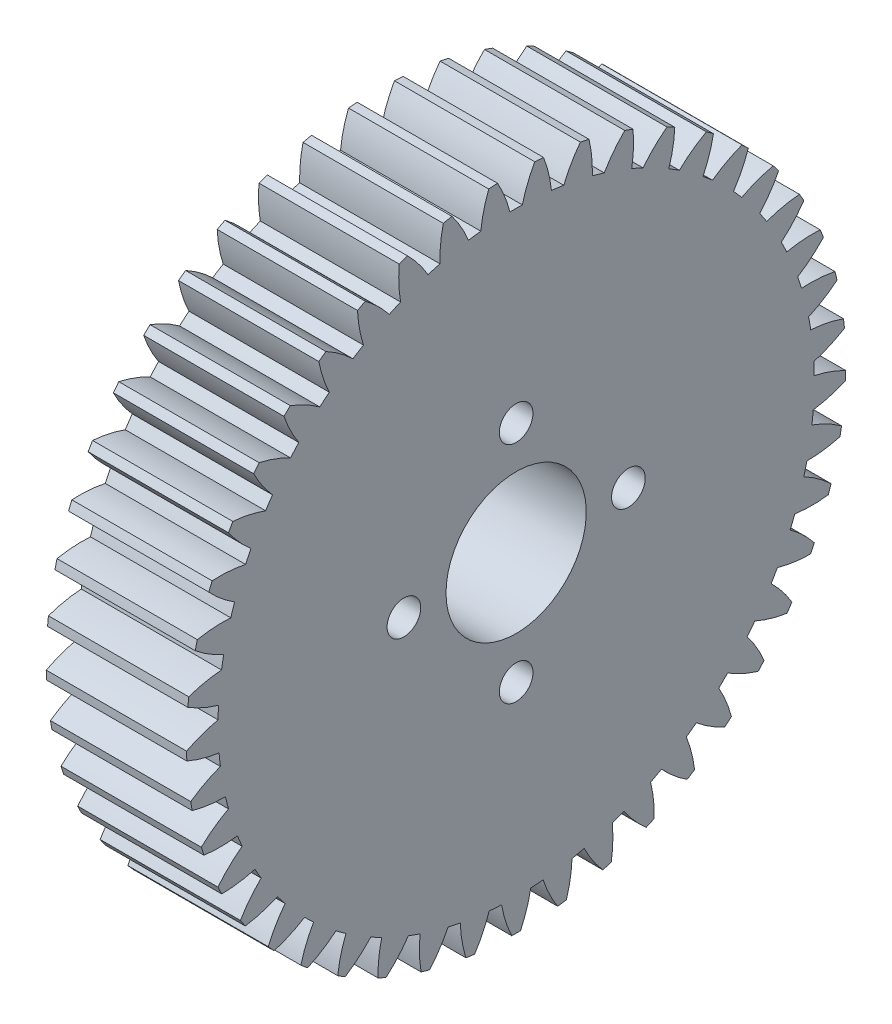
SolidWorks part; units mm, degrees
ref_plane "Plane1" through (0, 0, 0) normal (0, 0, 1) x (1, 0, 0)
ref_plane "Plane2" through (0, 0, 0) normal (0, 1, 0) x (1, 0, 0)
ref_plane "Plane3" through (0, 0, 0) normal (1, 0, 0) x (0, 0, -1)
sketch "HoldingSke" plane through (0, 0, 0) normal (0, 1, 0) x (1, 0, 0)
  line L0 (0, 0) -> (0.7071, -0.7071)
  line L1 (-15, 0) -> (100, 0) construction
  line L2 (0, 0) -> (-2.1039, 2.3779)
  line L3 (0, 0) -> (-11.863, 4.5341)
  line L4 (0, 0) -> (6.1066, 6.1066)
  line L5 (0, 0) -> (-46.8476, -17.4728)
  line L6 (0, 0) -> (-8.2896, -5.593)
  line L7 (-2.1039, 2.3779) -> (8.6586, 51.2059)
  line L8 (-76.2, 54.61) -> (-74.4, 54.61)
  line L9 (-71.009, 38.7566) -> (-53.1078, 45.2721)
  line L10 (-76.2, 71.12) -> (104.1128, 71.12)
  line L11 (0, 0) -> (-10, 0)
  line L12 (-76.2, 101.6) -> (-76.162, 101.6)
  line L13 (24.9733, 27.94) -> (52.9518, 28.4284)
  line L14 (24.9733, 27.94) -> (24.9743, 27.94)
  line L15 (24.9733, 27.94) -> (100.4006, 29.5858)
  line L16 (-63.627, -1) -> (-12.827, -1)
  circle A0 centre (0, 0) radius 5
  circle A1 centre (0, 0) radius 21.249
  circle A2 centre (0, 0) radius 37.5
  circle A3 centre (0, 0) radius 5
  dimension "MHD" = 42.498
  dimension "Hub_dia" = 75
  dimension "Bore" = 10
  dimension "MBD" = 10
  dimension "Num_teeth" = 45
  dimension "Pitch" = 1
  dimension "Overall_len" = 50
  dimension "Show_teeth" = 45
  dimension "Thickness" = 10
  dimension "OAL" = 50.0001
  dimension "T_dim" = 1.8
  dimension "Ap" = 20
  dimension "H" = 19.05
  dimension "Pitch_radius" = 180.3128
  dimension "Width" = 10
  dimension "Backlash" = 0.038
  dimension "Addendum_fac" = 1
  dimension "Dedendum_fac" = 1.25
  dimension "Clearance_fac" = 0.25
  dimension "Dedendum_add" = 0.001
  dimension "Module" = 1
sketch "BasProSke" plane through (0, 0, 0) normal (0, 1, 0) x (1, 0, 0)
  line L0 (-10, 0) -> (60, 0) construction
  line L1 (0, 0) -> (0, 23.5)
  line L2 (0, 0) -> (10, 0)
  line L3 (10, 0) -> (10, 23.5)
  line L4 (10, 23.5) -> (0, 23.5)
  dimension "Thickness" = 10
  dimension "Diameter" = 47
revolve "Base-Revolve" add sketch "BasProSke" angle 360 about L0
sketch "TooCutSke" plane through (0, 0, 0) normal (1, 0, 0) x (0, 0, -1)
  line L1 (0, 0) -> (0, 107) construction
  line L2 (0, 0) -> (-0.8517, 22.4839) construction
  line L3 (0, 0) -> (-3.1374, 44.8675) construction
  line L4 (-0.8517, 22.4839) -> (-1.5687, 22.4337) construction
  arc A0 (0.4426, 21.2444) -> (-0.4426, 21.2444) centre (0, 0) ccw
  arc A1 (1.3407, 23.4872) -> (-1.3407, 23.4872) centre (0, 0) ccw
  circle A2 centre (0, 0) radius 22.5 construction
  circle A3 centre (0, 0) radius 21.1431 construction
  arc A4 (-0.4426, 21.2444) -> (-1.3407, 23.4872) centre (-9.1711, 19.0505) ccw
  arc A5 (1.3407, 23.4872) -> (0.4426, 21.2444) centre (9.1711, 19.0505) ccw
  dimension "Root_dia" = 42.498
  dimension "Overcut_dia" = 47.0508
  dimension "Pitch_dia" = 45
  dimension "Base_dia" = 42.2862
  dimension "Flank_rad" = 9
  dimension "Half_ang" = 4
  dimension "Half_CT" = 0.7187
extrude "ToothCut" cut sketch "TooCutSke" along normal through all
fillet "Breaks" [suppressed] radius 0.02
fillet "RootFillets" [suppressed] radius 0.251
pattern_circular "TeethCuts" count 45 every 8 about axis through (-10, 0, 0) along (1, 0, 0) of "ToothCut", "RootFillets", "Breaks"
sketch "HubNeaOneSke" plane through (0, 0, 0) normal (-1, 0, 0) x (0, 0, 1)
  circle A0 centre (0, 0) radius 21.249
  dimension "Diameter" = 42.498
extrude "HubNearOne" [suppressed] add sketch "HubNeaOneSke" along normal blind 40.0001
sketch "HubNeaBotSke" plane through (0, 0, 0) normal (-1, 0, 0) x (0, 0, 1)
  circle A0 centre (0, 0) radius 21.249
  dimension "Diameter" = 42.498
extrude "HubNearBoth" [suppressed] add sketch "HubNeaBotSke" along normal blind 20
ref_plane "FarPln" through (10, 0, 0) normal (1, 0, 0) x (0, 0, -1)
sketch "HubFarSke" plane through (10, 0, 0) normal (1, 0, 0) x (0, 0, -1)
  circle A0 centre (0, 0) radius 21.249
  dimension "Diameter" = 42.498
extrude "HubFar" [suppressed] add sketch "HubFarSke" along normal blind 20
sketch "BorSke" plane through (0, 0, 0) normal (1, 0, 0) x (0, 0, -1)
  circle A0 centre (0, 0) radius 5
  dimension "Diameter" = 10
extrude "Bore" cut sketch "BorSke" along normal mid plane 100.0001
sketch "KeySke" plane through (0, 0, 0) normal (1, 0, 0) x (0, 0, -1)
  line L0 (-2, 0) -> (-2, 6.8)
  line L1 (-2, 6.8) -> (2, 6.8)
  line L2 (2, 6.8) -> (2, 0)
  line L3 (0, 0) -> (0, 34) construction
  line L4 (-2, 0) -> (2, 0)
  dimension "Offset" = 6.8
  dimension "Width" = 4
extrude "Keyway" [suppressed] cut sketch "KeySke" along normal mid plane 100.0001
pattern_circular "Keyway2" [suppressed] count 2 every 90 about axis through (-10, 0, 0) along (1, 0, 0)
hole_wizard "Dégagement M21" positions "Esquisse1" profile "Esquisse2" hole size "M2" standard "ISO" end condition up to next
sketch "Esquisse1" plane through (10, 0, 0) normal (1, 0, 0) x (0, 0, -1)
  point P0 (0, 8)
  point P6 (8, 0)
  point P7 (0, -8)
  point P8 (-8, 0)
  point P9 (0, 0)
  dimension "D1" = 4
sketch "Esquisse2" plane through (10, 8, 0) normal (0, 1, 0) x (0, 0, -1)
  line L0 (0, 0) -> (0, 10)
  line L1 (0, 10) -> (1.2, 10)
  line L2 (1.2, 10) -> (1.2, 0)
  line L5 (1.2, 0) -> (0, 0)
  line L11 (0, -6.35) -> (0, 107.95) construction
  dimension "Diamètre du perçage jusqu'au prochain" = 2.4
  dimension "Profondeur du perçage jusqu'au prochain" = 10
equation "' \"Module@HoldingSke\" = 6.35"
equation "' \"Num_teeth@HoldingSke\" = 12"
equation "' \"Ap@HoldingSke\" =  20"
equation "' \"Ap@HoldingSke\" = 20"
equation "' \"Width@HoldingSke\" = 0.5 * 25.4"
equation "' \"Hub_dia@HoldingSke\"= 1 * 25.4"
equation "' \"Hub_dia@HoldingSke\" = 1 * 25.4"
equation "' \"Overall_len@HoldingSke\" = 1.0 * 25.4"
equation "' \"Bore@HoldingSke\" = 0.75 * 25.4"
equation "' \"T_dim@HoldingSke\" = 0.1 * 25.4"
equation "' \"Width@KeySke\" = 0.25 * 25.4"
equation "' \"Show_teeth@HoldingSke\" = 13"
equation "' \"Backlash@HoldingSke\" = 0.009 * 25.4"
equation "' \"Addendum_fac@HoldingSke\" = 1.0"
equation "' \"Dedendum_fac@HoldingSke\" = 1.25"
equation "' \"Dedendum_add@HoldingSke\" = 0.00005 * 25.4"
equation "' \"Clearance_fac@HoldingSke\" = 0.25"
equation "\"Pitch@HoldingSke\" = 1 / \"Module@HoldingSke\""
equation "\"Overcut_dia@TooCutSke\" = (\"Num_teeth@HoldingSke\" + 2 * \"Addendum_fac@HoldingSke\") / \"Pitch@HoldingSke\" + 0.002 * 25.4"
equation "\"Pitch_dia@TooCutSke\" = \"Num_teeth@HoldingSke\" / \"Pitch@HoldingSke\""
equation "\"Base_dia@TooCutSke\" = \"Num_teeth@HoldingSke\" / \"Pitch@HoldingSke\" * cos((\"Ap@HoldingSke\"  * 3.14159265 / 180))"
equation "\"Root_dia@TooCutSke\" = (\"Num_teeth@HoldingSke\" + 2) / \"Pitch@HoldingSke\" - 2 * (\"Addendum_fac@HoldingSke\" + \"Dedendum_fac@HoldingSke\") / \"Pitch@HoldingSke\" - \"Dedendum_add@HoldingSke\" * 2"
equation "\"Half_ang@TooCutSke\" = 180 / \"Num_teeth@HoldingSke\""
equation "\"Half_CT@TooCutSke\" = \"Num_teeth@HoldingSke\" / \"Pitch@HoldingSke\" * sin((3.14159265 / 2 / \"Num_teeth@HoldingSke\")) / 2 - 7 * \"Backlash@HoldingSke\" / 4"
equation "\"Flank_rad@TooCutSke\" = \"Num_teeth@HoldingSke\" / \"Pitch@HoldingSke\" / 5"
equation "\"Radius@RootFillets\" = \"Clearance_fac@HoldingSke\" / \"Pitch@HoldingSke\" + \"Dedendum_add@HoldingSke\""
equation "\"Break_rad@Breaks\" = 0.02 / \"Pitch@HoldingSke\""
equation "\"Thickness@HoldingSke\" = \"Width@HoldingSke\""
equation "\"OAL@HoldingSke\" = \"Thickness@HoldingSke\""
equation "\"MHD@HoldingSke\" = (\"Num_teeth@HoldingSke\" + 2) / \"Pitch@HoldingSke\" - 2 * (\"Addendum_fac@HoldingSke\" + \"Dedendum_fac@HoldingSke\")  / \"Pitch@HoldingSke\" - \"Dedendum_add@HoldingSke\" * 2"
equation "\"MBD@HoldingSke\" = (\"Num_teeth@HoldingSke\" + 2) / \"Pitch@HoldingSke\" - 2 * (\"Addendum_fac@HoldingSke\" + \"Dedendum_fac@HoldingSke\")  / \"Pitch@HoldingSke\" - \"Dedendum_add@HoldingSke\" * 2 - 0.002 * 25.4"
equation "\"MHD@HoldingSke\" = ((sgn( \"MHD@HoldingSke\" - \"Hub_dia@HoldingSke\" )-1)*( \"MHD@HoldingSke\" - \"Hub_dia@HoldingSke\" ))/-2+ \"Hub_dia@HoldingSke\""
equation "\"MBD@HoldingSke\" = ((sgn( \"MBD@HoldingSke\" - \"Bore@HoldingSke\" )-1)*( \"MBD@HoldingSke\" - \"Bore@HoldingSke\" ))/-2+ \"Bore@HoldingSke\""
equation "\"OAL@HoldingSke\" = ((sgn( \"OAL@HoldingSke\" - \"Overall_len@HoldingSke\" )+1)*( \"OAL@HoldingSke\" - \"Overall_len@HoldingSke\" ))/2 + \"Overall_len@HoldingSke\" + 0.000002 * 25.4"
equation "\"Num_teeth@TeethCuts\" = int( \"Show_teeth@HoldingSke\" ) + 1"
equation "\"Num_teeth@TeethCuts\" = ((sgn( \"Num_teeth@TeethCuts\" - \"Num_teeth@HoldingSke\" )-1)*( \"Num_teeth@TeethCuts\" - \"Num_teeth@HoldingSke\" ))/-2+ \"Num_teeth@HoldingSke\""
equation "\"Num_teeth@TeethCuts\" = ((sgn( \"Num_teeth@TeethCuts\" - 2.0)+1)*( \"Num_teeth@TeethCuts\" - 2.0))/2 +2.0"
equation "\"Angle@TeethCuts\" = 360.0 / \"Num_teeth@HoldingSke\""
equation "\"Diameter@BasProSke\" = (\"Num_teeth@HoldingSke\" + 2 * \"Addendum_fac@HoldingSke\") / \"Pitch@HoldingSke\""
equation "\"Thickness@BasProSke\"  = \"Thickness@HoldingSke\""
equation "' \"Fillet_rad@BasProSke\" =  \"Thickness@HoldingSke\" * 0.05"
equation "' \"Fillet_rad@BasProSke\" = \"Thickness@HoldingSke\" * 0.05"
equation "\"MHD@HoldingSke\" = ((sgn( \"MHD@HoldingSke\" - \"Root_dia@TooCutSke\" )-1)*( \"MHD@HoldingSke\" - \"Root_dia@TooCutSke\" ))/-2+ \"Root_dia@TooCutSke\""
equation "\"Diameter@HubNeaOneSke\" = \"MHD@HoldingSke\""
equation "\"Length@HubNearOne\" = \"OAL@HoldingSke\" - \"Thickness@BasProSke\""
equation "\"Diameter@HubNeaBotSke\" = \"MHD@HoldingSke\""
equation "\"Length@HubNearBoth\" = ( \"OAL@HoldingSke\" - \"Thickness@BasProSke\" ) / 2.0"
equation "\"Thickness@FarPln\" = \"Thickness@BasProSke\""
equation "\"Diameter@HubFarSke\" = \"MHD@HoldingSke\""
equation "\"Length@HubFar\" = ( \"OAL@HoldingSke\" - \"Thickness@BasProSke\" ) / 2.0"
equation "\"Diameter@BorSke\" = \"MBD@HoldingSke\""
equation "\"D1@Bore\" = \"OAL@HoldingSke\" * 2.0"
equation "\"D1@Keyway\" = \"OAL@HoldingSke\" * 2.0"
equation "\"Offset@KeySke\" = \"T_dim@HoldingSke\" + \"MBD@HoldingSke\" / 2.0"
